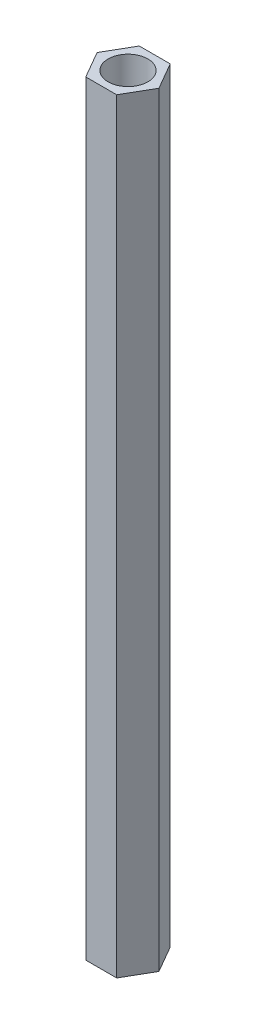
SolidWorks part; units mm, degrees
material "黄铜"
ref_plane "前视基准面" through (0, 0, 0) normal (0, 0, 1) x (1, 0, 0)
ref_plane "上视基准面" through (0, 0, 0) normal (0, 1, 0) x (1, 0, 0)
ref_plane "右视基准面" through (0, 0, 0) normal (1, 0, 0) x (0, 0, -1)
sketch "草图1" plane through (0, 0, 0) normal (0, 1, 0) x (1, 0, 0)
  line L1 (4.0415, 0) -> (2.0207, 3.5)
  line L2 (2.0207, 3.5) -> (-2.0207, 3.5)
  line L3 (-2.0207, 3.5) -> (-4.0415, 0)
  line L4 (-4.0415, 0) -> (-2.0207, -3.5)
  line L5 (-2.0207, -3.5) -> (2.0207, -3.5)
  line L6 (2.0207, -3.5) -> (4.0415, 0)
  circle A0 centre (0, 0) radius 3.5 construction
  dimension "D1" = 7
extrude "凸台-拉伸1" add sketch "草图1" along normal blind 100
sketch "草图2" plane through (0, 100, 0) normal (0, 1, 0) x (1, 0, 0)
  circle A0 centre (0, 0) radius 2.6
  dimension "D1" = 5.2
extrude "切除-拉伸1" cut sketch "草图2" against normal through all
ref_plane "基准面1" through (0, 90, 0) normal (0, 1, 0) x (1, 0, 0)
sketch "草图3" plane through (0, 90, 0) normal (0, 1, 0) x (1, 0, 0)
  circle A0 centre (0, 0) radius 2.6 construction
  circle A1 centre (0, 0) radius 2.6
extrude "凸台-拉伸2" add sketch "草图3" against normal offset from surface (80 mm away) 10 up to face at (0, 0, 2.6)
